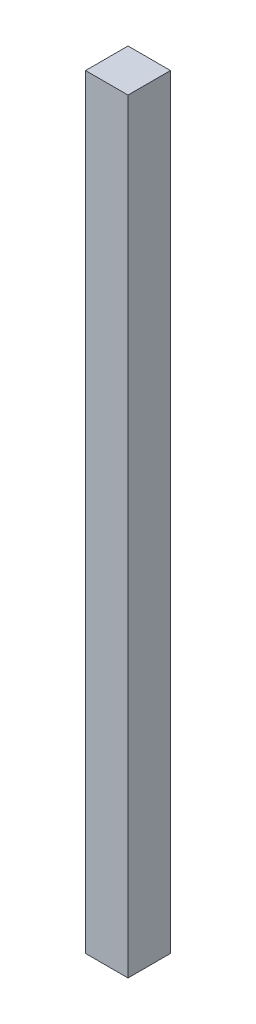
SolidWorks part; units mm, degrees
ref_plane "Plano frontal" through (0, 0, 0) normal (0, 0, 1) x (1, 0, 0)
ref_plane "Plano superior" through (0, 0, 0) normal (0, 1, 0) x (1, 0, 0)
ref_plane "Plano direito" through (0, 0, 0) normal (1, 0, 0) x (0, 0, -1)
sketch "Esboço2" plane through (0, 0, 0) normal (0, 1, 0) x (1, 0, 0)
  line L1 (-50, 29.0761) -> (0, 29.0761)
  line L2 (-50, 29.0761) -> (-50, -20.9239)
  line L3 (-50, -20.9239) -> (0, -20.9239)
  line L4 (0, 29.0761) -> (0, -20.9239)
  dimension "D1" = 50
  dimension "D2" = 50
extrude "Ressalto-extrusão1" add sketch "Esboço2" along normal blind 900 contours L1 L4 L3 L2
